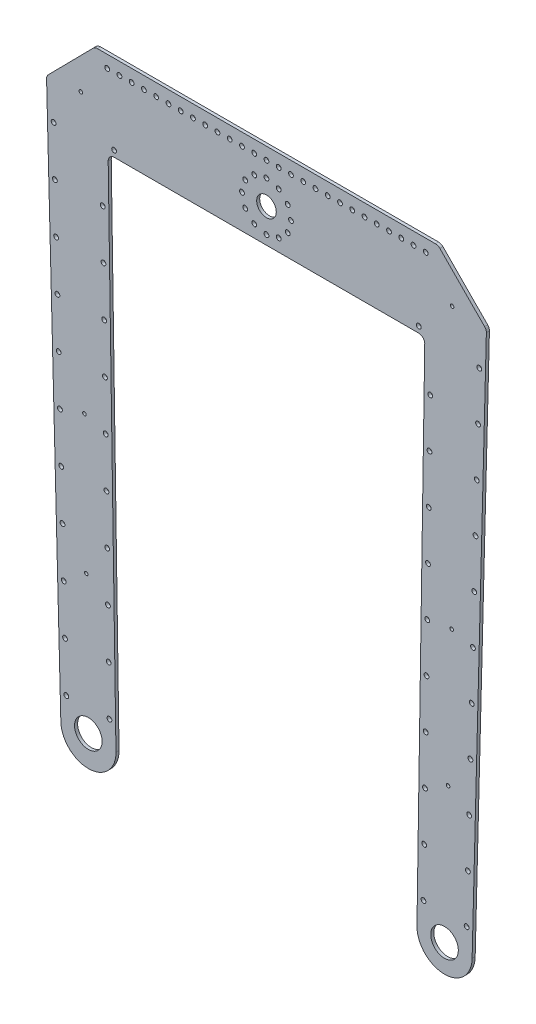
SolidWorks part; units mm, degrees
material "PPE"
ref_plane "Front Plane" through (0, 0, 0) normal (0, 0, 1) x (1, 0, 0)
ref_plane "Top Plane" through (0, 0, 0) normal (0, 1, 0) x (1, 0, 0)
ref_plane "Right Plane" through (0, 0, 0) normal (1, 0, 0) x (0, 0, -1)
sketch "Sketch1" plane through (0, 0, 0) normal (0, 0, 1) x (1, 0, 0)
  line L0 (25.4, 25.4) -> (25.4, 0)
  line L1 (0, 0) -> (508, 0) construction
  line L2 (0, 0) -> (0, 25.4) construction
  line L3 (0, 25.4) -> (508, 25.4) construction
  line L4 (508, 0) -> (508, 25.4) construction
  line L5 (482.6, 25.4) -> (482.6, 0)
  line L6 (25.4, 25.4) -> (482.6, 25.4)
  line L7 (25.4, 0) -> (40.894, -596.9)
  line L8 (254, 25.4) -> (254, 0) construction
  line L9 (482.6, 0) -> (467.106, -596.9)
  line L10 (88.9, 0) -> (98.0406, -596.4621)
  line L11 (419.1, 0) -> (409.9594, -596.4621)
  line L12 (88.9, 0) -> (419.1, 0)
  line L13 (89.8731, -63.5) -> (418.1269, -63.5)
  line L14 (254, -28.575) -> (254, -3.175) construction
  line L19 (33.4004, -63.5) -> (34.7186, -114.2829) construction
  line L20 (34.7186, -114.2829) -> (84.2809, -112.9964) construction
  line L21 (84.2809, -112.9964) -> (85.0593, -163.7904) construction
  line L22 (473.2814, -114.2829) -> (423.7191, -112.9964) construction
  line L23 (423.7191, -112.9964) -> (422.9407, -163.7904) construction
  line L24 (76.2, 25.4) -> (26.0593, -25.4)
  line L25 (431.8, 25.4) -> (481.9407, -25.4)
  line L26 (88.9, 12.7) -> (101.6, 12.7) construction
  circle A0 centre (69.469, -596.9) radius 50.8 construction
  circle A1 centre (438.531, -596.9) radius 50.8 construction
  arc A2 (40.894, -596.9) -> (98.0406, -596.4621) centre (69.469, -596.9) ccw
  circle A3 centre (69.469, -596.9) radius 14.2875 construction
  circle A4 centre (438.531, -596.9) radius 14.2875
  arc A5 (467.106, -596.9) -> (409.9594, -596.4621) centre (438.531, -596.9) cw
  circle A6 centre (254, -28.575) radius 10.16
  circle A7 centre (254, -28.575) radius 25.4 construction
  circle A8 centre (254, -3.175) radius 2.4892
  circle A9 centre (266.7, -6.578) radius 2.4892
  circle A10 centre (275.997, -15.875) radius 2.4892
  circle A11 centre (279.4, -28.575) radius 2.4892
  circle A12 centre (275.997, -41.275) radius 2.4892
  circle A13 centre (266.7, -50.572) radius 2.4892
  circle A14 centre (254, -53.975) radius 2.4892
  circle A15 centre (241.3, -50.572) radius 2.4892
  circle A16 centre (232.003, -41.275) radius 2.4892
  circle A17 centre (228.6, -28.575) radius 2.4892
  circle A18 centre (232.003, -15.875) radius 2.4892
  circle A19 centre (241.3, -6.578) radius 2.4892
  circle A22 centre (254, -28.575) radius 192.5 construction
  circle A24 centre (438.531, -596.9) radius 142.5 construction
  circle A25 centre (442.2191, -454.4477) radius 142.5 construction
  circle A28 centre (442.2191, -454.4477) radius 1.8288
  circle A29 centre (61.6125, -21.9961) radius 1.8288
  circle A32 centre (33.4004, -63.5) radius 2.4892
  circle A33 centre (33.4004, -63.5) radius 6.35 construction
  circle A34 centre (34.7186, -114.2829) radius 2.4892
  circle A35 centre (36.0368, -165.0658) radius 2.4892
  circle A36 centre (37.355, -215.8487) radius 2.4892
  circle A37 centre (38.6732, -266.6316) radius 2.4892
  circle A38 centre (39.9914, -317.4145) radius 2.4892
  circle A39 centre (41.3096, -368.1974) radius 2.4892
  circle A40 centre (42.6278, -418.9803) radius 2.4892
  circle A41 centre (43.946, -469.7632) radius 2.4892
  circle A42 centre (45.2642, -520.546) radius 2.4892
  circle A43 centre (46.5824, -571.3289) radius 2.4892
  circle A44 centre (474.5996, -63.5) radius 2.4892
  circle A45 centre (461.4176, -571.3289) radius 2.4892
  circle A46 centre (462.7358, -520.546) radius 2.4892
  circle A47 centre (464.054, -469.7632) radius 2.4892
  circle A48 centre (465.3722, -418.9803) radius 2.4892
  circle A49 centre (466.6904, -368.1974) radius 2.4892
  circle A50 centre (468.0086, -317.4145) radius 2.4892
  circle A51 centre (469.3268, -266.6316) radius 2.4892
  circle A52 centre (470.645, -215.8487) radius 2.4892
  circle A53 centre (471.9632, -165.0658) radius 2.4892
  circle A54 centre (473.2814, -114.2829) radius 2.4892
  circle A55 centre (96.1266, -57.15) radius 2.4892
  circle A57 centre (411.8734, -57.15) radius 2.4892
  circle A58 centre (84.2809, -112.9964) radius 2.4892
  circle A59 centre (85.0593, -163.7904) radius 2.4892
  circle A60 centre (85.8377, -214.5845) radius 2.4892
  circle A61 centre (86.6161, -265.3785) radius 2.4892
  circle A62 centre (87.3945, -316.1725) radius 2.4892
  circle A63 centre (88.1729, -366.9666) radius 2.4892
  circle A64 centre (88.9513, -417.7606) radius 2.4892
  circle A65 centre (89.7297, -468.5546) radius 2.4892
  circle A66 centre (90.5082, -519.3487) radius 2.4892
  circle A67 centre (91.2866, -570.1427) radius 2.4892
  circle A68 centre (423.7191, -112.9964) radius 2.4892
  circle A69 centre (422.9407, -163.7904) radius 2.4892
  circle A70 centre (422.1623, -214.5845) radius 2.4892
  circle A71 centre (421.3839, -265.3785) radius 2.4892
  circle A72 centre (420.6055, -316.1725) radius 2.4892
  circle A73 centre (419.8271, -366.9666) radius 2.4892
  circle A74 centre (419.0487, -417.7606) radius 2.4892
  circle A75 centre (418.2703, -468.5546) radius 2.4892
  circle A76 centre (417.4918, -519.3487) radius 2.4892
  circle A77 centre (416.7134, -570.1427) radius 2.4892
  circle A82 centre (61.6125, -21.9961) radius 287.02 construction
  circle A84 centre (67.2405, -451.4792) radius 142.5 construction
  circle A86 centre (69.4024, -593.9628) radius 14.2875
  circle A87 centre (67.2405, -451.4792) radius 1.8288
  circle A88 centre (65.3733, -308.9915) radius 1.8288
  circle A89 centre (446.3875, -21.9961) radius 1.8288
  circle A90 centre (446.3875, -21.9961) radius 290 construction
  circle A91 centre (445.9168, -311.9957) radius 1.8288
  circle A92 centre (88.9, 12.7) radius 2.4892
  circle A93 centre (101.6, 12.7) radius 2.4892
  circle A94 centre (114.3, 12.7) radius 2.4892
  circle A95 centre (127, 12.7) radius 2.4892
  circle A96 centre (139.7, 12.7) radius 2.4892
  circle A97 centre (152.4, 12.7) radius 2.4892
  circle A98 centre (165.1, 12.7) radius 2.4892
  circle A99 centre (177.8, 12.7) radius 2.4892
  circle A100 centre (190.5, 12.7) radius 2.4892
  circle A101 centre (203.2, 12.7) radius 2.4892
  circle A102 centre (215.9, 12.7) radius 2.4892
  circle A103 centre (228.6, 12.7) radius 2.4892
  circle A104 centre (241.3, 12.7) radius 2.4892
  circle A105 centre (254, 12.7) radius 2.4892
  circle A106 centre (266.7, 12.7) radius 2.4892
  circle A107 centre (279.4, 12.7) radius 2.4892
  circle A108 centre (292.1, 12.7) radius 2.4892
  circle A109 centre (304.8, 12.7) radius 2.4892
  circle A110 centre (317.5, 12.7) radius 2.4892
  circle A111 centre (330.2, 12.7) radius 2.4892
  circle A112 centre (342.9, 12.7) radius 2.4892
  circle A113 centre (355.6, 12.7) radius 2.4892
  circle A114 centre (368.3, 12.7) radius 2.4892
  circle A115 centre (381, 12.7) radius 2.4892
  circle A116 centre (393.7, 12.7) radius 2.4892
  circle A117 centre (406.4, 12.7) radius 2.4892
  circle A118 centre (419.1, 12.7) radius 2.4892
  dimension "D4" = 101.6
  dimension "D6" = 267.462
  dimension "D7" = 28.575
  dimension "D8" = 28.575
  dimension "D11" = 20.32
  dimension "D13" = 50.8
  dimension "D14" = 4.9784
  dimension "D20" = 385
  dimension "D21" = 285
  dimension "D22" = 580
  dimension "D24" = 28.575
  dimension "D25" = 4.9784
  dimension "D26" = 12.7
  dimension "D39" = 574.04
  dimension "D40" = 28.575
  dimension "D42" = 3.6576
  dimension "D43" = 12.7
  dimension "D44" = 4.9784
  dimension "D1" = 508
  dimension "D2" = 25.4
  dimension "D3" = 25.4
  dimension "D5" = 596.9
  dimension "D9" = 63.5
  dimension "D10" = 63.5
  dimension "D12" = 28.575
  dimension "D23" = 28.575
  dimension "D27" = 11
  dimension "D28" = 50.8
  dimension "D29" = 6.35
  dimension "D30" = 6.35
  dimension "D31" = 6.35
  dimension "D33" = 50.8
  dimension "D34" = 6.35
  dimension "D36" = 50.8
  dimension "D37" = 50.8
  dimension "D38" = 50.8
  dimension "D41" = 28.575
  dimension "D46" = 12.7
  dimension "D32" = 10
  dimension "D35" = 10
  dimension "D45" = 27
  dimension "D16" = 12
extrude "Boss-Extrude1" add sketch "Sketch1" along normal blind 3.175
fillet "Fillet1" radius 6.35 6 edges at (418.1269, -63.5, 1.5875) (89.8731, -63.5, 1.5875) (481.9407, -25.4, 1.5875) (431.8, 25.4, 1.5875) (76.2, 25.4, 1.5875) (26.0593, -25.4, 1.5875)
sketch "Sketch2" plane through (0, 0, 3.175) normal (0, 0, 1) x (1, 0, 0)
  line L0 (456.8703, 0) -> (476.0123, -253.7903)
  line L1 (433.6648, 23.5107) -> (480.042, -23.4764) construction
  line L2 (481.8705, -28.1019) -> (467.106, -596.9) construction
  line L3 (78.8546, 25.4) -> (429.1454, 25.4) construction
  dimension "D1" = 25.4
